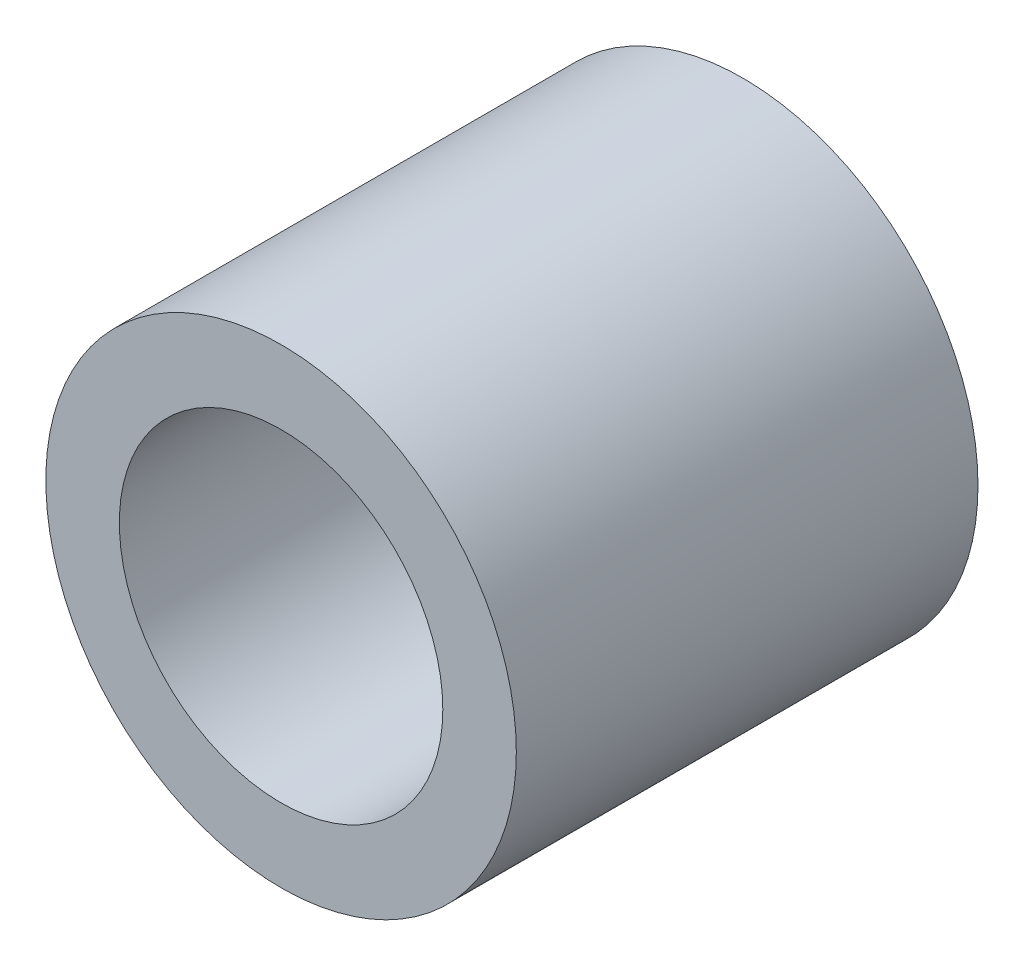
SolidWorks part; units mm, degrees
ref_plane "Front Plane" through (0, 0, 0) normal (0, 0, 1) x (1, 0, 0)
ref_plane "Top Plane" through (0, 0, 0) normal (0, 1, 0) x (1, 0, 0)
ref_plane "Right Plane" through (0, 0, 0) normal (1, 0, 0) x (0, 0, -1)
sketch "Sketch1" plane through (0, 0, 0) normal (0, 0, 1) x (1, 0, 0)
  circle A0 centre (0, 0) radius 4
  circle A1 centre (0, 0) radius 2.75
  dimension "D1" = 8
  dimension "D2" = 5.5
extrude "Boss-Extrude1" add sketch "Sketch1" along normal blind 7.85
